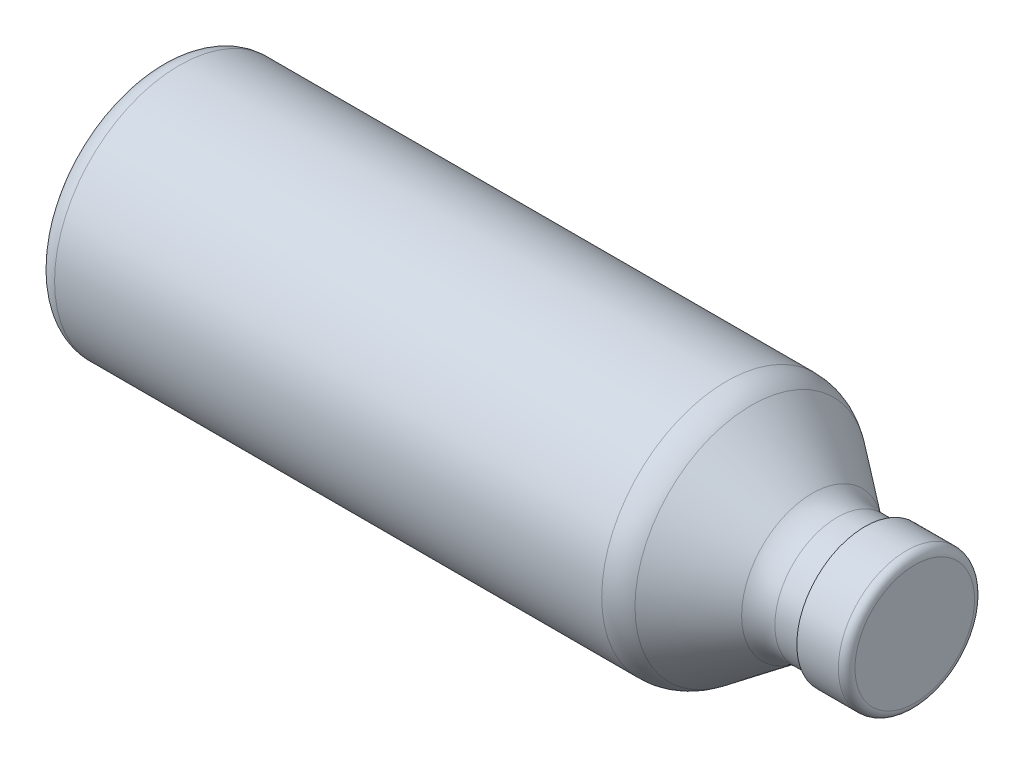
SolidWorks part; units mm, degrees
ref_plane "前视基准面" through (0, 0, 0) normal (0, 0, 1) x (1, 0, 0)
ref_plane "上视基准面" through (0, 0, 0) normal (0, 1, 0) x (1, 0, 0)
ref_plane "右视基准面" through (0, 0, 0) normal (1, 0, 0) x (0, 0, -1)
sketch "草图1" plane through (0, 0, 0) normal (0, 0, 1) x (1, 0, 0)
  line L0 (0, 0) -> (105.9064, 0) construction
  line L1 (180, 15) -> (163.3333, 15)
  line L2 (157.3333, 17) -> (142.6667, 28)
  line L3 (136.6667, 30) -> (0, 30)
  line L4 (0, 30) -> (0, 0)
  line L5 (0, 0) -> (180, 0)
  line L6 (180, 0) -> (180, 15)
  arc A0 (163.3333, 15) -> (157.3333, 17) centre (163.3333, 25) cw
  arc A1 (142.6667, 28) -> (136.6667, 30) centre (136.6667, 20) ccw
  point P10 (160, 15)
  point P13 (140, 30)
  dimension "D6" = 10
  dimension "D1" = 30
  dimension "D2" = 180
  dimension "D3" = 20
  dimension "D4" = 30
  dimension "D5" = 20
revolve "旋转1" add sketch "草图1" angle 360 about L0
fillet "圆角1" radius 5 1 edges at (0, 0, 30)
shell "抽壳1" thickness 1
sketch "草图2" plane through (180, 0, 0) normal (1, 0, 0) x (0, 0, -1)
  circle A0 centre (0, 0) radius 15
  circle A1 centre (0, 0) radius 16.3916
extrude "凸台-拉伸1" add sketch "草图2" against normal blind 10
sketch "草图3" plane through (180, 0, 0) normal (1, 0, 0) x (0, 0, -1)
  circle A0 centre (0, 0) radius 16.3916
extrude "凸台-拉伸2" add sketch "草图3" along normal blind 2
fillet "圆角2" radius 2 1 edges at (182, 0, -16.3916)
